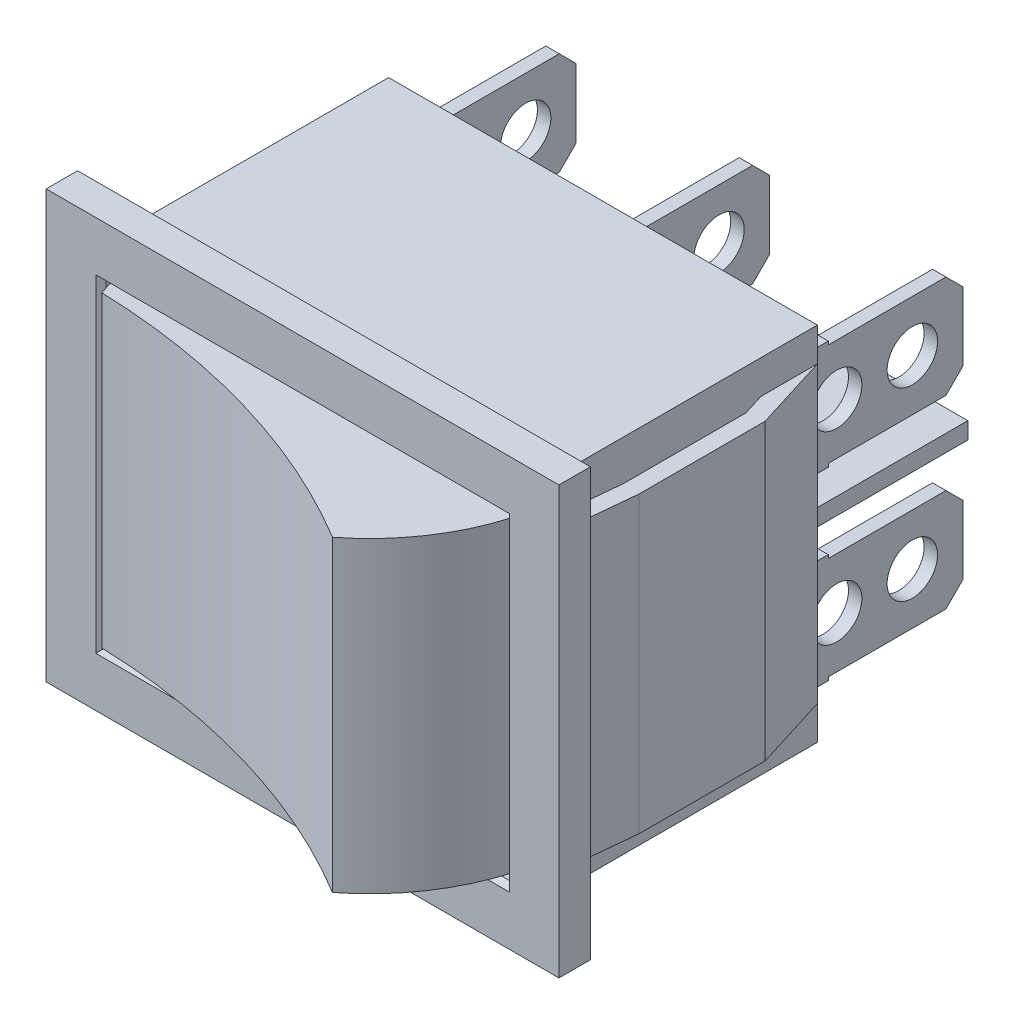
SolidWorks part; units mm, degrees
ref_plane "Front Plane" through (0, 0, 0) normal (0, 0, 1) x (1, 0, 0)
ref_plane "Top Plane" through (0, 0, 0) normal (0, 1, 0) x (1, 0, 0)
ref_plane "Right Plane" through (0, 0, 0) normal (1, 0, 0) x (0, 0, -1)
sketch "Sketch1" plane through (0, 0, 0) normal (0, 0, 1) x (1, 0, 0)
  line L1 (-12.75, 10.75) -> (12.75, 10.75)
  line L2 (-12.75, 10.75) -> (-12.75, -10.75)
  line L3 (-12.75, -10.75) -> (12.75, -10.75)
  line L4 (12.75, 10.75) -> (12.75, -10.75)
  line L5 (-12.75, 10.75) -> (12.75, -10.75) construction
  line L6 (-12.75, -10.75) -> (12.75, 10.75) construction
  point P0 (0, 0)
  dimension "D1" = 21.5
  dimension "D2" = 25.5
extrude "Boss-Extrude1" add sketch "Sketch1" along normal blind 16
sketch "Sketch3" plane through (0, 0, 16) normal (0, 0, 1) x (1, 0, 0)
  line L1 (-15.25, 12.7) -> (15.25, 12.7)
  line L2 (-15.25, 12.7) -> (-15.25, -12.7)
  line L3 (-15.25, -12.7) -> (15.25, -12.7)
  line L4 (15.25, 12.7) -> (15.25, -12.7)
  line L5 (-15.25, 12.7) -> (15.25, -12.7) construction
  line L6 (-15.25, -12.7) -> (15.25, 12.7) construction
  point P0 (0, 0)
  dimension "D1" = 25.4
  dimension "D2" = 30.5
extrude "Boss-Extrude3" add sketch "Sketch3" along normal blind 1.87
sketch "Sketch4" plane through (0, 0, 0) normal (0, 0, -1) x (-1, 0, 0)
  line L1 (-11.9, 0.5) -> (11.9, 0.5)
  line L2 (-11.9, 0.5) -> (-11.9, -0.5)
  line L3 (-11.9, -0.5) -> (11.9, -0.5)
  line L4 (11.9, 0.5) -> (11.9, -0.5)
  line L5 (-11.9, 0.5) -> (11.9, -0.5) construction
  line L6 (-11.9, -0.5) -> (11.9, 0.5) construction
  point P0 (0, 0)
  dimension "D1" = 1
  dimension "D2" = 23.8
extrude "Boss-Extrude4" add sketch "Sketch4" along normal blind 9.8
sketch "Sketch5" plane through (0, 0, 0) normal (0, 0, -1) x (-1, 0, 0)
  line L0 (-11.9, -0.5) -> (11.9, -0.5) construction
  line L1 (11.1, -2.25) -> (11.9, -2.25)
  line L2 (11.1, -2.25) -> (11.1, -8.75)
  line L3 (11.1, -8.75) -> (11.9, -8.75)
  line L4 (11.9, -2.25) -> (11.9, -8.75)
  line L5 (11.1, -2.25) -> (11.9, -8.75) construction
  line L6 (11.1, -8.75) -> (11.9, -2.25) construction
  line L7 (-0.4, -8.75) -> (0.4, -8.75)
  line L8 (-0.4, -8.75) -> (-0.4, -2.25)
  line L9 (-0.4, -2.25) -> (0.4, -2.25)
  line L10 (0.4, -8.75) -> (0.4, -2.25)
  line L11 (-0.4, -8.75) -> (0.4, -2.25) construction
  line L12 (-0.4, -2.25) -> (0.4, -8.75) construction
  line L13 (-11.9, -2.25) -> (-11.1, -2.25)
  line L14 (-11.9, -2.25) -> (-11.9, -8.75)
  line L15 (-11.9, -8.75) -> (-11.1, -8.75)
  line L16 (-11.1, -2.25) -> (-11.1, -8.75)
  line L17 (-11.9, -2.25) -> (-11.1, -8.75) construction
  line L18 (-11.9, -8.75) -> (-11.1, -2.25) construction
  point P0 (11.5, -5.5)
  point P5 (-11.5, -5.5)
  point P6 (0, -5.5)
  dimension "D1" = 6.5
  dimension "D2" = 0.8
  dimension "D3" = 6.5
  dimension "D4" = 0.8
  dimension "D5" = 6.5
  dimension "D6" = 0.8
  dimension "D7" = 5
extrude "Boss-Extrude5" add sketch "Sketch5" along normal blind 9.5
sketch "Sketch6" plane through (11.9, 0, 0) normal (1, 0, 0) x (0, 0, -1)
  line L1 (9.5, -2.25) -> (1.5, -2.25)
  line L2 (9.5, -2.25) -> (9.5, -2.45)
  line L3 (9.5, -2.45) -> (1.5, -2.45)
  line L4 (1.5, -2.25) -> (1.5, -2.45)
  line L5 (9.5, -8.75) -> (1.5, -8.75)
  line L6 (9.5, -8.75) -> (9.5, -8.55)
  line L7 (9.5, -8.55) -> (1.5, -8.55)
  line L8 (1.5, -8.75) -> (1.5, -8.55)
  dimension "D1" = 0.2
  dimension "D2" = 8
extrude "Cut-Extrude1" cut sketch "Sketch6" against normal through all
chamfer "Chamfer1" distance 1 angle 45 6 edges at (-11.5, -8.55, -9.5) (-11.5, -2.45, -9.5) (0, -8.55, -9.5) (0, -2.45, -9.5) (11.5, -2.45, -9.5) (11.5, -8.55, -9.5)
sketch "Sketch7" plane through (11.9, 0, 0) normal (1, 0, 0) x (0, 0, -1)
  line L0 (1.5, -2.25) -> (0, -2.25) construction
  line L1 (9.5, -3.45) -> (9.5, -7.55) construction
  circle A0 centre (6.5, -5.5) radius 1.5
  circle A1 centre (2, -5.5) radius 1.5
  dimension "D1" = 3.25
  dimension "D2" = 3
  dimension "D3" = 3
  dimension "D4" = 4.5
extrude "Cut-Extrude2" cut sketch "Sketch7" against normal through all
ref_plane "Plane1" through (0, 0, 0) normal (0, -1, 0) x (-1, 0, 0)
mirror "Mirror1" about plane through (0, 0, 0) normal (0, -1, 0) of "Cut-Extrude2", "Chamfer1", "Cut-Extrude1", "Boss-Extrude5"
sketch "Sketch8" plane through (0, 10.75, 0) normal (0, 1, 0) x (1, 0, 0)
  line L0 (-12.75, 0) -> (-14.15, -4.5)
  line L1 (-12.75, -16) -> (-12.75, 0) construction
  line L2 (-14.15, -4.5) -> (-14.15, -12)
  line L3 (-14.15, -12) -> (-13.7549, -16)
  line L4 (15.25, -16) -> (-15.25, -16) construction
  line L5 (-13.7549, -16) -> (-12.75, -16)
  line L6 (-12.75, -16) -> (-13.15, -11.9507)
  line L7 (-13.15, -11.9507) -> (-13.15, -4.652)
  line L8 (-13.15, -4.652) -> (-12.75, -3.3662)
  line L9 (-12.75, -3.3662) -> (-12.75, 0)
  line L10 (12.75, 0) -> (-12.75, 0) construction
  line L11 (12.75, -16) -> (-12.75, -16) construction
  dimension "D1" = 1
  dimension "D2" = 1
  dimension "D3" = 1
  dimension "D4" = 1.4
  dimension "D5" = 4.5
  dimension "D6" = 4
extrude "Boss-Extrude6" add sketch "Sketch8" against normal offset from surface (17.5 mm away) 2 from offset 2 up to face at (0, -10.75, 8) offset against normal yes
ref_plane "Plane2" through (0, 0, 0) normal (-1, 0, 0) x (0, 0, 1)
mirror "Mirror2" about plane through (0, 0, 0) normal (-1, 0, 0) of "Boss-Extrude6"
sketch "Sketch9" plane through (0, 0, 17.87) normal (0, 0, 1) x (1, 0, 0)
  line L0 (-12, -9.45) -> (-12, 9.45)
  line L1 (-15.25, -12.7) -> (15.25, -12.7)
  line L2 (-15.25, -12.7) -> (-15.25, 12.7)
  line L3 (-15.25, 12.7) -> (15.25, 12.7)
  line L4 (15.25, -12.7) -> (15.25, 12.7)
  line L5 (-12, 9.45) -> (12, 9.45)
  line L6 (12, -9.45) -> (12, 9.45)
  line L7 (-12, -9.45) -> (12, -9.45)
  dimension "D1" = 3.25
extrude "Cut-Extrude3" cut sketch "Sketch9" against normal blind 5 contours L0 L7 L6 L5
sketch "Sketch10" plane through (0, 0, 0) normal (0, -1, 0) x (-1, 0, 0)
  line L0 (15.25, -17.87) -> (-15.25, -17.87) construction
  circle A0 centre (0, -13.87) radius 12.5
  dimension "D1" = 4
  dimension "D2" = 25
extrude "Boss-Extrude7" add sketch "Sketch10" along normal mid plane 18.3
sketch "Sketch11" plane through (0, 0, 0) normal (0, -1, 0) x (-1, 0, 0)
  circle A0 centre (13, -58) radius 40
  dimension "D1" = 80
  dimension "D2" = 58
  dimension "D3" = 13
extrude "Cut-Extrude4" cut sketch "Sketch11" against normal through all both and the other way through all
chamfer "Chamfer2" distance 0.3 angle 45 4 edges at (0, -9.45, 17.87) (12, 0, 17.87) (0, 9.45, 17.87) (-12, 0, 17.87)
